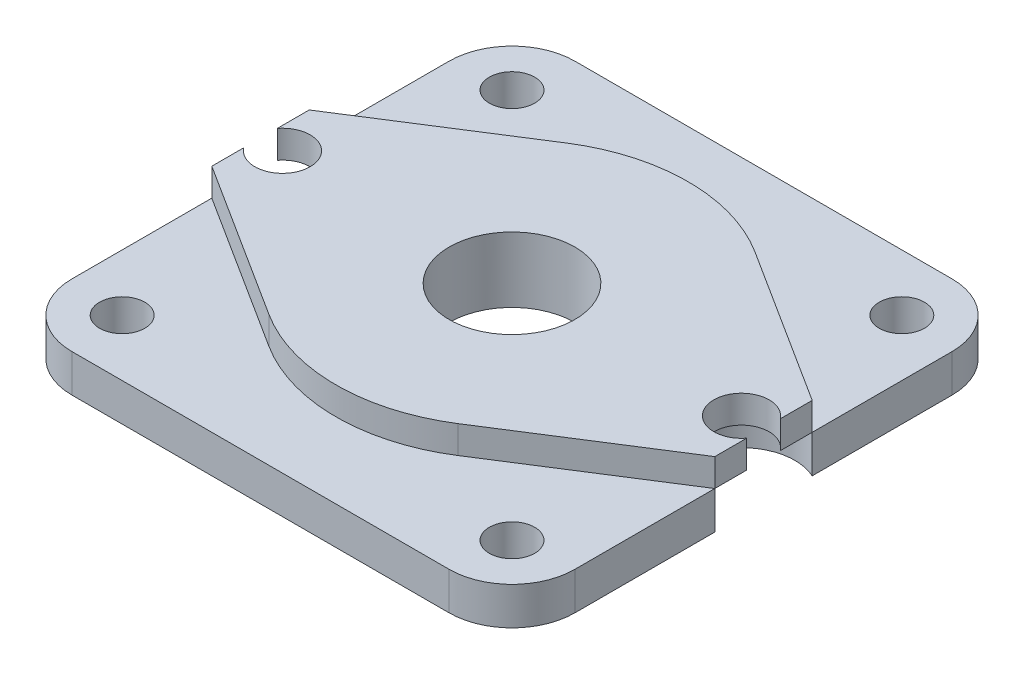
SolidWorks part; units mm, degrees
ref_plane "前视基准面" through (0, 0, 0) normal (0, 0, 1) x (1, 0, 0)
ref_plane "上视基准面" through (0, 0, 0) normal (0, 1, 0) x (1, 0, 0)
ref_plane "右视基准面" through (0, 0, 0) normal (1, 0, 0) x (0, 0, -1)
sketch "草图1" plane through (0, 0, 0) normal (0, 1, 0) x (1, 0, 0)
  line L0 (20, -3.873) -> (20, -15)
  line L1 (-15, 20) -> (15, 20)
  line L2 (-20, 15) -> (-20, 3.873)
  line L3 (-15, -20) -> (15, -20)
  line L4 (20, 15) -> (20, 3.873)
  line L5 (-20, -3.873) -> (-20, -15)
  circle A0 centre (-15.5, 15.5) radius 1.8
  circle A1 centre (15.5, 15.5) radius 1.8
  circle A2 centre (-15.5, -15.5) radius 1.8
  circle A3 centre (15.5, -15.5) radius 1.8
  arc A4 (-20, 15) -> (-15, 20) centre (-15, 15) cw
  arc A5 (20, 15) -> (15, 20) centre (15, 15) ccw
  arc A6 (15, -20) -> (20, -15) centre (15, -15) ccw
  arc A7 (-20, -15) -> (-15, -20) centre (-15, -15) ccw
  circle A8 centre (0, 0) radius 5
  arc A9 (-20, -3.873) -> (-20, 3.873) centre (-18.25, 0) ccw
  arc A10 (20, 3.873) -> (20, -3.873) centre (18.25, 0) ccw
  point P30 (0, 0)
  dimension "D1" = 5
  dimension "D2" = 5
  dimension "D3" = 5
  dimension "D4" = 5
extrude "凸台-拉伸1" add sketch "草图1" along normal blind 3
sketch "草图2" plane through (0, 3, 0) normal (0, 1, 0) x (1, 0, 0)
  line L0 (-20, 3.873) -> (-7.5123, 11.8138)
  line L1 (-20, -3.873) -> (-7.5123, -11.8138)
  line L2 (20, 3.873) -> (7.5123, 11.8138)
  line L3 (20, -3.873) -> (7.5123, -11.8138)
  line L4 (-20, 15) -> (-20, 3.873) construction
  line L5 (-20, 3.873) -> (-20, 1.3332)
  line L6 (-20, -3.873) -> (-20, -1.3332)
  line L7 (20, 3.873) -> (20, 1.3332)
  line L8 (20, -1.3332) -> (20, -3.873)
  arc A0 (-7.5123, -11.8138) -> (7.5123, -11.8138) centre (0, 0) ccw
  arc A1 (7.5123, 11.8138) -> (-7.5123, 11.8138) centre (0, 0) ccw
  arc A2 (20, 1.3332) -> (20, -1.3332) centre (18.25, 0) ccw
  arc A3 (-20, -1.3332) -> (-20, 1.3332) centre (-18.25, 0) ccw
  arc A4 (-20, -3.873) -> (-20, 3.873) centre (-18.25, 0) ccw construction
extrude "凸台-拉伸2" add sketch "草图2" along normal blind 2.2
sketch "草图3" plane through (0, 3, 0) normal (0, -1, 0) x (1, 0, 0)
  circle A0 centre (0, 0) radius 5
extrude "切除-拉伸1" cut sketch "草图3" against normal blind 2.2
